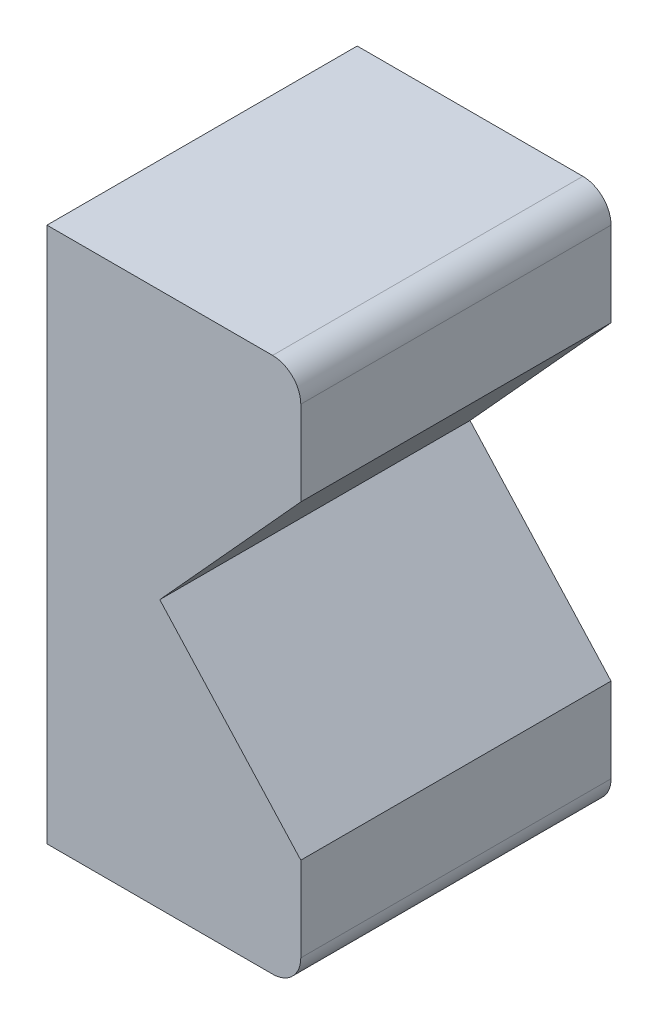
SolidWorks part; units mm, degrees
ref_plane "Спереди" through (0, 0, 0) normal (0, 0, 1) x (1, 0, 0)
ref_plane "Сверху" through (0, 0, 0) normal (0, 1, 0) x (1, 0, 0)
ref_plane "Справа" through (0, 0, 0) normal (1, 0, 0) x (0, 0, -1)
sketch "Эскиз1" plane through (0, 0, 0) normal (0, 0, 1) x (1, 0, 0)
  line L0 (0, 0) -> (0, 19)
  line L1 (0, 19) -> (8, 19)
  line L2 (9, 18) -> (9, 15)
  line L3 (0, 0) -> (8, 0)
  line L4 (9, 1) -> (9, 4)
  line L6 (9, 15) -> (4, 9.5)
  line L7 (9, 4) -> (4, 9.5)
  arc A0 (9, 18) -> (8, 19) centre (8, 18) ccw
  arc A1 (9, 1) -> (8, 0) centre (8, 1) cw
  dimension "D1" = 1
extrude "Бобышка-Вытянуть1" add sketch "Эскиз1" along normal blind 11
